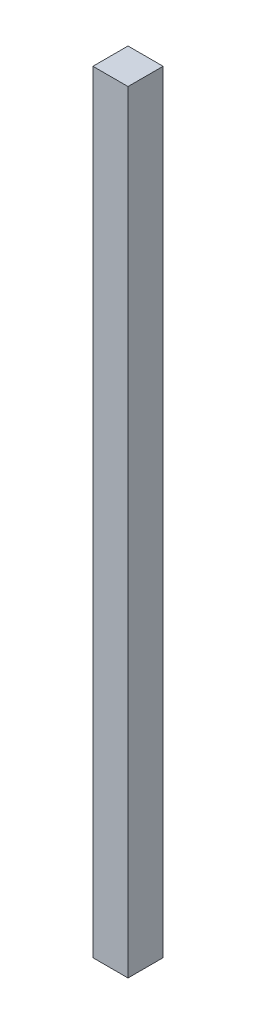
SolidWorks part; units mm, degrees
ref_plane "Front Plane" through (0, 0, 0) normal (0, 0, 1) x (1, 0, 0)
ref_plane "Top Plane" through (0, 0, 0) normal (0, 1, 0) x (1, 0, 0)
ref_plane "Right Plane" through (0, 0, 0) normal (1, 0, 0) x (0, 0, -1)
sketch "Sketch1" plane through (0, 0, 0) normal (0, 1, 0) x (1, 0, 0)
  line L1 (-41.7324, 32.1292) -> (-16.3324, 32.1292)
  line L2 (-41.7324, 32.1292) -> (-41.7324, 6.7292)
  line L3 (-41.7324, 6.7292) -> (-16.3324, 6.7292)
  line L4 (-16.3324, 32.1292) -> (-16.3324, 6.7292)
  dimension "D1" = 25.4
  dimension "D2" = 25.4
extrude "Boss-Extrude1" add sketch "Sketch1" along normal blind 558.8
